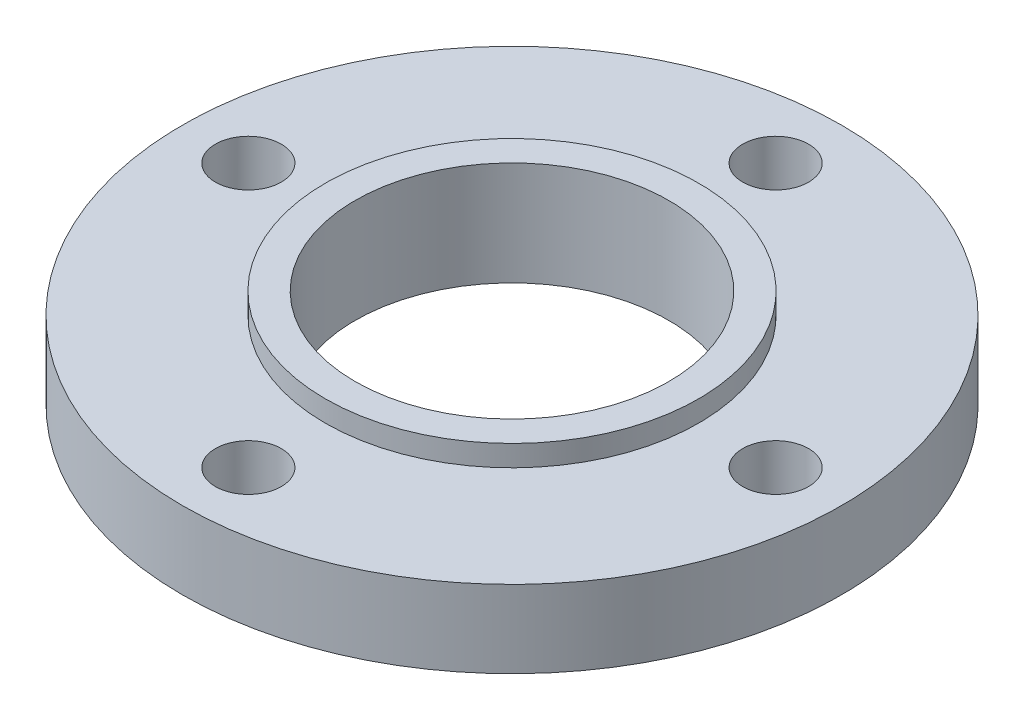
SolidWorks part; units mm, degrees
ref_plane "Front Plane" through (0, 0, 0) normal (0, 0, 1) x (1, 0, 0)
ref_plane "Top Plane" through (0, 0, 0) normal (0, 1, 0) x (1, 0, 0)
ref_plane "Right Plane" through (0, 0, 0) normal (1, 0, 0) x (0, 0, -1)
sketch "Sketch1" plane through (0, 0, 0) normal (0, 1, 0) x (1, 0, 0)
  circle A0 centre (0, 0) radius 3.75
  dimension "D1" = 7.5
extrude "Boss-Extrude1" add sketch "Sketch1" along normal blind 0.88
sketch "Sketch2" plane through (0, 0, 0) normal (0, 1, 0) x (1, 0, 0)
  circle A0 centre (0, 0) radius 2.125
  dimension "D1" = 4.25
extrude "Boss-Extrude2" add sketch "Sketch2" along normal blind 1.12
sketch "Sketch3" plane through (0, 0, 0) normal (0, 1, 0) x (1, 0, 0)
  circle A0 centre (0, 0) radius 2.5
  dimension "D1" = 5
extrude "Boss-Extrude3" add sketch "Sketch3" against normal blind 0.0625
sketch "Sketch4" plane through (0, 0, 0) normal (0, 1, 0) x (1, 0, 0)
  circle A0 centre (0, 0) radius 1.785
  dimension "D1" = 3.57
extrude "Cut-Extrude1" cut sketch "Sketch4" against normal blind 1.0625 and the other way blind 3
sketch "Sketch6" plane through (0, 0, 0) normal (0, 0, 1) x (1, 0, 0)
  line L0 (0, -0.1307) -> (0, 1.1638) construction
sketch "Sketch7" plane through (0, 0, 0) normal (0, 1, 0) x (1, 0, 0)
  circle A0 centre (0, 3) radius 0.375
  dimension "D1" = 0.75
  dimension "D2" = 3
extrude "Cut-Extrude2" cut sketch "Sketch7" along normal blind 3.0625
pattern_circular "CirPattern1" count 4 over 360 about axis through (0, 0, 0) along (0, 1, 0) of "Cut-Extrude2"
scale "Scale1" scale about centroid uniform scaling yes scale factor 25.4
